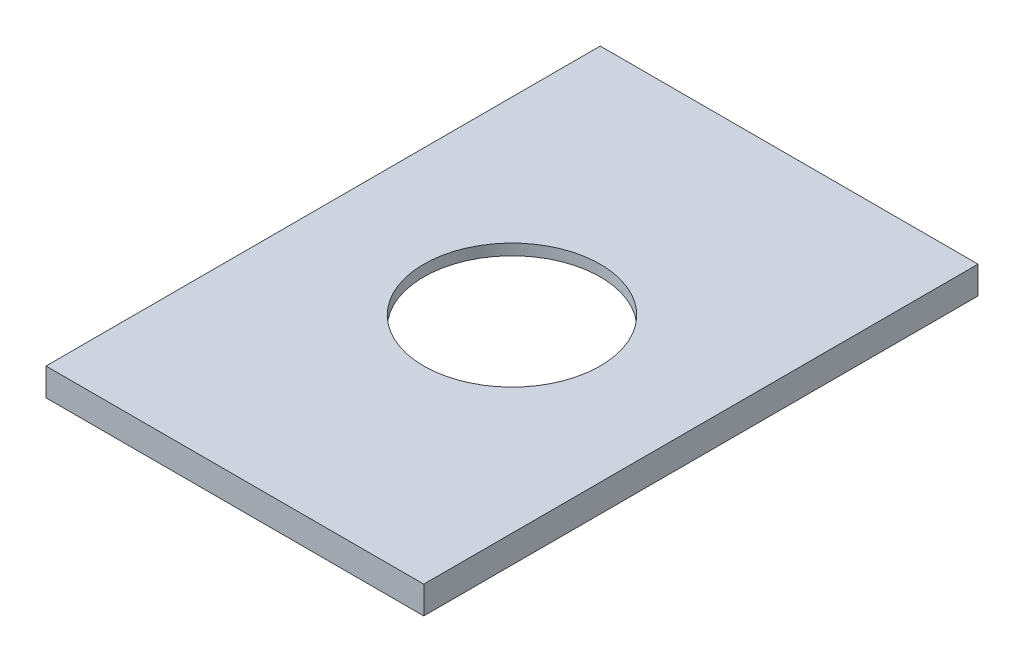
SolidWorks part; units mm, degrees
ref_plane "Alzado" through (0, 0, 0) normal (0, 0, 1) x (1, 0, 0)
ref_plane "Planta" through (0, 0, 0) normal (0, 1, 0) x (1, 0, 0)
ref_plane "Vista lateral" through (0, 0, 0) normal (1, 0, 0) x (0, 0, -1)
sketch "Croquis1" plane through (0, 0, 0) normal (0, 1, 0) x (1, 0, 0)
  line L0 (7.75, 37) -> (7.75, -59.5) construction
  line L1 (-24.5, 37) -> (40, 37)
  line L2 (-24.5, 37) -> (-24.5, -59.5)
  line L3 (-24.5, -59.5) -> (40, -59.5)
  line L4 (40, 37) -> (40, -59.5)
  line L6 (-6.25, -6.1) -> (-24.5, -6.1) construction
  line L7 (-4.5, -39.5) -> (20, -39.5) construction
  circle A4 centre (7.75, -11.25) radius 16
  point P0 (0, 0)
  point P10 (0, -17.55)
  dimension "D8" = 20
  dimension "D3" = 32
  dimension "D12" = 64.5
  dimension "D20" = 96.5
  dimension "D22" = 33.4
extrude "Saliente-Extruir4" add sketch "Croquis1" along normal blind 2
sketch "Croquis2" plane through (0, 0, 0) normal (0, -1, 0) x (1, 0, 0)
  line L5 (-24.5, 59.5) -> (40, 59.5)
  line L6 (-24.5, 59.5) -> (-24.5, -37)
  line L7 (-24.5, -37) -> (40, -37)
  line L8 (42, -39) -> (42, 61.5)
  line L9 (42, 61.5) -> (-26.5, 61.5)
  line L10 (-26.5, 61.5) -> (-26.5, -39)
  line L11 (-26.5, -39) -> (42, -39)
  line L12 (42, -39) -> (42, 61.5)
  line L13 (42, 61.5) -> (-26.5, 61.5)
  line L14 (-26.5, 61.5) -> (-26.5, -39)
  line L15 (-26.5, -39) -> (42, -39)
  line L16 (40, 59.5) -> (40, -37)
  dimension "D1" = 2
extrude "Saliente-Extruir5" add sketch "Croquis2" along normal blind 3 and the other way up to surface (2 mm away) other way up to face at (7.75, 2, 11.25)
